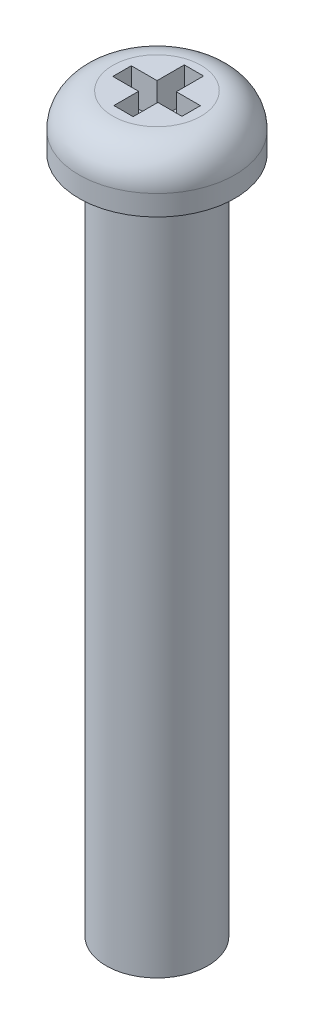
SolidWorks part; units mm, degrees
ref_plane "前基準面" through (0, 0, 0) normal (0, 0, 1) x (1, 0, 0)
ref_plane "上基準面" through (0, 0, 0) normal (0, 1, 0) x (1, 0, 0)
ref_plane "右基準面" through (0, 0, 0) normal (1, 0, 0) x (0, 0, -1)
sketch "草圖2" plane through (0, 0, 0) normal (0, 0, 1) x (1, 0, 0)
  line L0 (0, 0) -> (1.5, 0)
  line L1 (1.5, 0) -> (1.5, 20)
  line L2 (1.5, 20) -> (2.3, 20)
  line L3 (2.3, 20) -> (2.3, 20.6)
  line L4 (1.3, 21.6) -> (0, 21.6)
  line L5 (0, 21.6) -> (0, 0)
  arc A0 (2.3, 20.6) -> (1.3, 21.6) centre (1.3, 20.6) ccw
  dimension "D4" = 1
  dimension "D1" = 1.5
  dimension "D2" = 2.3
  dimension "D3" = 0.6
  dimension "D5" = 20
revolve "旋轉1" add sketch "草圖2" angle 360 about L5
sketch "草圖3" plane through (0, 21.6, 0) normal (0, 1, 0) x (1, 0, 0)
  line L0 (-0.2571, 0.2602) -> (-0.2571, 1.0636)
  line L1 (-0.2571, 1.0636) -> (0.3114, 1.0636)
  line L2 (0.3114, 1.0636) -> (0.3114, 0.2602)
  line L3 (0.3114, 0.2602) -> (1.0224, 0.2602)
  line L4 (1.0224, 0.2602) -> (1.0224, -0.2851)
  line L5 (1.0224, -0.2851) -> (0.3114, -0.2851)
  line L6 (0.3114, -0.2851) -> (0.3114, -1.0133)
  line L7 (0.3114, -1.0133) -> (-0.2571, -1.0133)
  line L8 (-0.2571, -1.0133) -> (-0.2571, -0.2851)
  line L9 (-0.2571, -0.2851) -> (-1.0163, -0.2851)
  line L10 (-1.0163, -0.2851) -> (-1.0163, 0.2602)
  line L11 (-1.0163, 0.2602) -> (-0.2571, 0.2602)
  point P2 (1.0224, 0.2663)
  point P13 (-1.0163, 0.2602)
  point P14 (-0.2571, -1.0133)
extrude "除料-伸長1" cut sketch "草圖3" against normal blind 1
